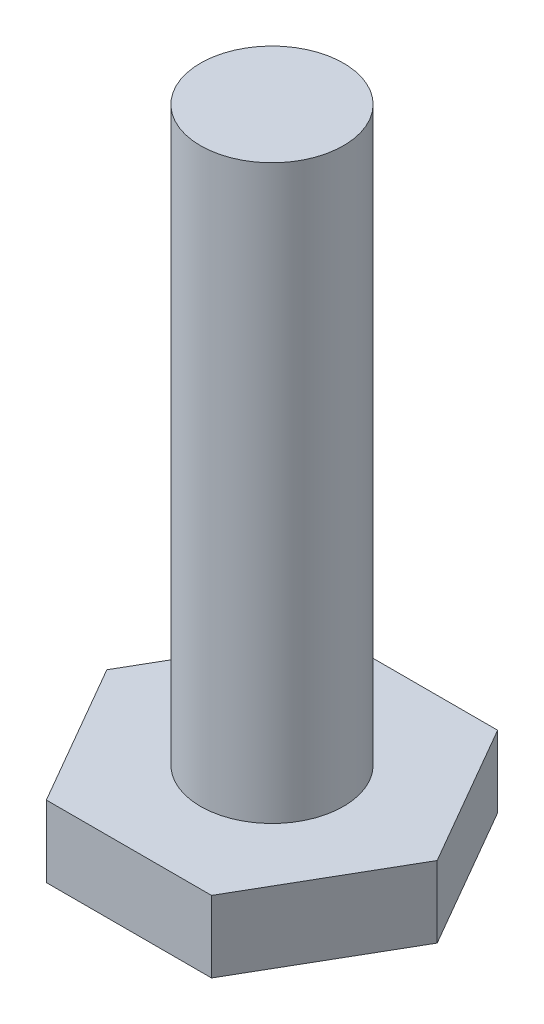
SolidWorks part; units mm, degrees
material "Plain Carbon Steel"
ref_plane "Front Plane" through (0, 0, 0) normal (0, 0, 1) x (1, 0, 0)
ref_plane "Top Plane" through (0, 0, 0) normal (0, 1, 0) x (1, 0, 0)
ref_plane "Right Plane" through (0, 0, 0) normal (1, 0, 0) x (0, 0, -1)
sketch "Sketch1" plane through (0, 0, 0) normal (0, 1, 0) x (1, 0, 0)
  line L1 (3.6662, 6.35) -> (-3.6662, 6.35)
  line L2 (-3.6662, 6.35) -> (-7.3323, 0)
  line L3 (-7.3323, 0) -> (-3.6662, -6.35)
  line L4 (-3.6662, -6.35) -> (3.6662, -6.35)
  line L5 (3.6662, -6.35) -> (7.3323, 0)
  line L6 (7.3323, 0) -> (3.6662, 6.35)
  circle A0 centre (0, 0) radius 6.35 construction
  dimension "D1" = 12.7
extrude "Boss-Extrude1" add sketch "Sketch1" along normal blind 3.175
sketch "Sketch2" plane through (0, 3.175, 0) normal (0, 1, 0) x (1, 0, 0)
  circle A0 centre (0, 0) radius 3.175
  dimension "D1" = 6.35
extrude "Boss-Extrude2" add sketch "Sketch2" along normal blind 25.4
